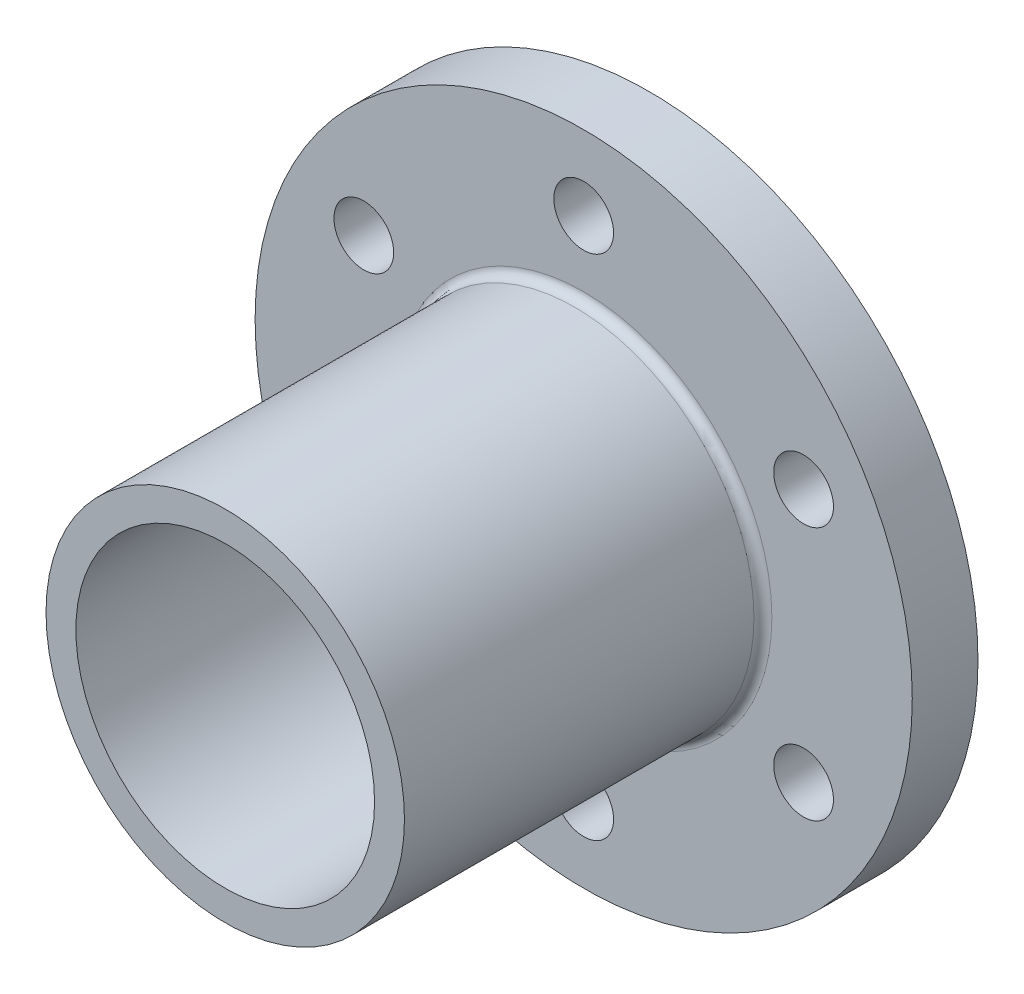
SolidWorks part; units mm, degrees
ref_plane "Front Plane" through (0, 0, 0) normal (0, 0, 1) x (1, 0, 0)
ref_plane "Top Plane" through (0, 0, 0) normal (0, 1, 0) x (1, 0, 0)
ref_plane "Right Plane" through (0, 0, 0) normal (1, 0, 0) x (0, 0, -1)
sketch "Sketch1" plane through (0, 0, 0) normal (0, 0, 1) x (1, 0, 0)
  circle A0 centre (0, 0) radius 110
  dimension "D1" = 220
extrude "Boss-Extrude1" add sketch "Sketch1" along normal blind 22
sketch "Sketch2" plane through (0, 0, 22) normal (0, 0, 1) x (1, 0, 0)
  circle A0 centre (0, 0) radius 60
  dimension "D1" = 120
extrude "Boss-Extrude2" add sketch "Sketch2" along normal blind 120
sketch "Sketch3" plane through (0, 0, 142) normal (0, 0, 1) x (1, 0, 0)
  circle A0 centre (0, 0) radius 50
  dimension "D1" = 100
extrude "Cut-Extrude1" cut sketch "Sketch3" against normal through all
sketch "Sketch4" plane through (0, 0, 22) normal (0, 0, 1) x (1, 0, 0)
  circle A0 centre (0, 85) radius 10
  circle A1 centre (73.6122, 42.5) radius 10
  circle A2 centre (73.6122, -42.5) radius 10
  circle A3 centre (0, -85) radius 10
  circle A4 centre (-73.6122, -42.5) radius 10
  circle A5 centre (-73.6122, 42.5) radius 10
  point P15 (0, 0)
  dimension "D1" = 20
  dimension "D2" = 85
  dimension "D3" = 6
extrude "Cut-Extrude2" cut sketch "Sketch4" against normal through all
fillet "Fillet1" radius 3 1 edges at (60, 0, 22)
